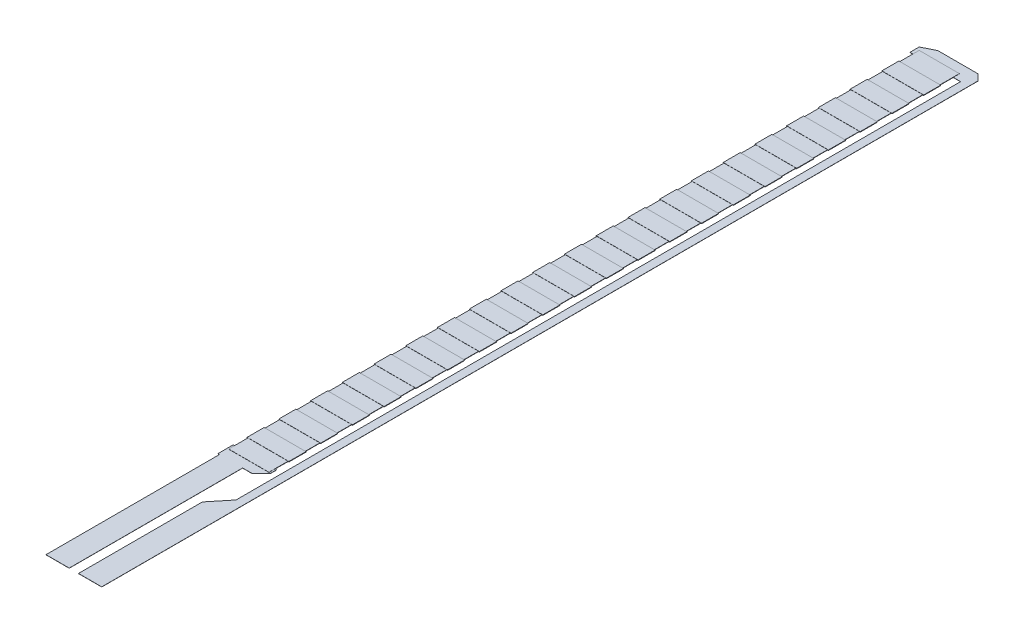
SolidWorks part; units mm, degrees
ref_plane "Front Plane" through (0, 0, 0) normal (0, 0, 1) x (1, 0, 0)
ref_plane "Top Plane" through (0, 0, 0) normal (0, 1, 0) x (1, 0, 0)
ref_plane "Right Plane" through (0, 0, 0) normal (1, 0, 0) x (0, 0, -1)
sketch "Sketch1" plane through (0, 13.0256, 0) normal (0, 1, 0) x (1, 0, 0)
  line L0 (-52.7883, -54.2802) -> (-46.4383, -54.2802) construction
  line L1 (-49.1053, -54.2802) -> (-47.2003, -54.2802)
  line L2 (-49.1053, -54.2802) -> (-49.1053, -44.1202)
  line L3 (-52.0263, 17.6018) -> (-51.0103, 18.1098)
  line L4 (-47.2003, -54.2802) -> (-47.2003, -44.1202)
  line L5 (-46.4383, -54.2802) -> (-46.4383, 16.3572) construction
  line L6 (-52.7883, 16.3572) -> (-52.7883, -54.2802) construction
  line L7 (-47.8646, -42.5962) -> (-47.8646, 16.8398)
  line L8 (-49.8673, -40.0562) -> (-49.1053, -40.0562)
  line L9 (-47.2003, -42.5962) -> (-47.2003, 16.8398)
  line L10 (-47.8646, 16.8398) -> (-52.0263, 16.8398)
  line L11 (-47.2003, 16.8398) -> (-47.2003, 17.6018)
  line L12 (-47.7083, 18.1098) -> (-51.0103, 18.1098)
  line L13 (-52.0263, 16.8398) -> (-52.0263, 17.6018)
  line L14 (-51.7723, -54.2802) -> (-49.8673, -54.2802)
  line L15 (-51.7723, -54.2802) -> (-51.7723, -40.0562)
  line L16 (-51.8993, -40.0562) -> (-51.7723, -40.0562)
  line L17 (-49.8673, -54.2802) -> (-49.8673, -40.0562)
  line L18 (-51.8993, -40.0562) -> (-51.8993, -38.7862)
  line L19 (-51.8993, -38.7862) -> (-48.3433, -38.7862)
  line L20 (-48.3433, -39.2942) -> (-48.3433, -38.7862)
  line L21 (-49.1053, -40.0562) -> (-48.3433, -39.2942)
  line L22 (-49.1053, -44.1202) -> (-47.8646, -42.5962)
  line L23 (-47.2003, -42.5962) -> (-47.2003, -44.1202)
  line L24 (-47.7083, 18.1098) -> (-47.2003, 17.6018)
  dimension "D1" = 0.762
  dimension "D2" = 1.905
  dimension "D3" = 10.16
  dimension "D4" = 59.436
  dimension "D5" = 1.016
  dimension "D6" = 72.39
  dimension "D7" = 4.826
  dimension "D8" = 0.508
  dimension "D9" = 0.508
  dimension "D10" = 0.508
  dimension "D11" = 1.905
  dimension "D12" = 1.016
  dimension "D13" = 15.494
  dimension "D14" = 1.27
  dimension "D15" = 3.556
  dimension "D16" = 0.762
  dimension "D18" = 0.762
extrude "Boss-Extrude1" add sketch "Sketch1" along normal blind 0.0127
sketch "Sketch2" plane through (0, 13.0256, 0) normal (0, 1, 0) x (1, 0, 0)
  line L0 (-46.4383, -54.2802) -> (-46.4383, 16.3572) construction
  line L1 (-51.7723, -39.2942) -> (-48.4703, -39.2942)
  line L2 (-51.7723, -39.2942) -> (-51.7723, 17.3478)
  line L3 (-51.7723, 17.3478) -> (-48.4703, 17.3478)
  line L4 (-48.4703, -39.2942) -> (-48.4703, 17.3478)
  dimension "D1" = 3.302
  dimension "D2" = 2.032
  dimension "D3" = 56.642
  dimension "D4" = 14.986
extrude "Boss-Extrude2" add sketch "Sketch2" along normal blind 0.0254
sketch "Sketch3" plane through (0, 13.0256, 0) normal (0, 1, 0) x (1, 0, 0)
  line L0 (-51.7723, 17.3478) -> (-51.7723, -39.2942) construction
  line L1 (-51.8358, -36.3224) -> (-48.4068, -36.3224)
  line L2 (-51.8358, -36.3224) -> (-51.8358, -37.7194)
  line L3 (-51.8358, -37.7194) -> (-48.4068, -37.7194)
  line L4 (-48.4068, -36.3224) -> (-48.4068, -37.7194)
  line L5 (-51.7723, -39.2942) -> (-48.4703, -39.2942) construction
  dimension "D1" = 3.429
  dimension "D2" = 1.397
  dimension "D3" = 0.0635
  dimension "D4" = 1.5748
extrude "Boss-Extrude3" add sketch "Sketch3" along normal blind 0.0381
pattern_linear "LPattern1" count 21 spacing 2.6035 along (0, 0, -1) of "Boss-Extrude3"
